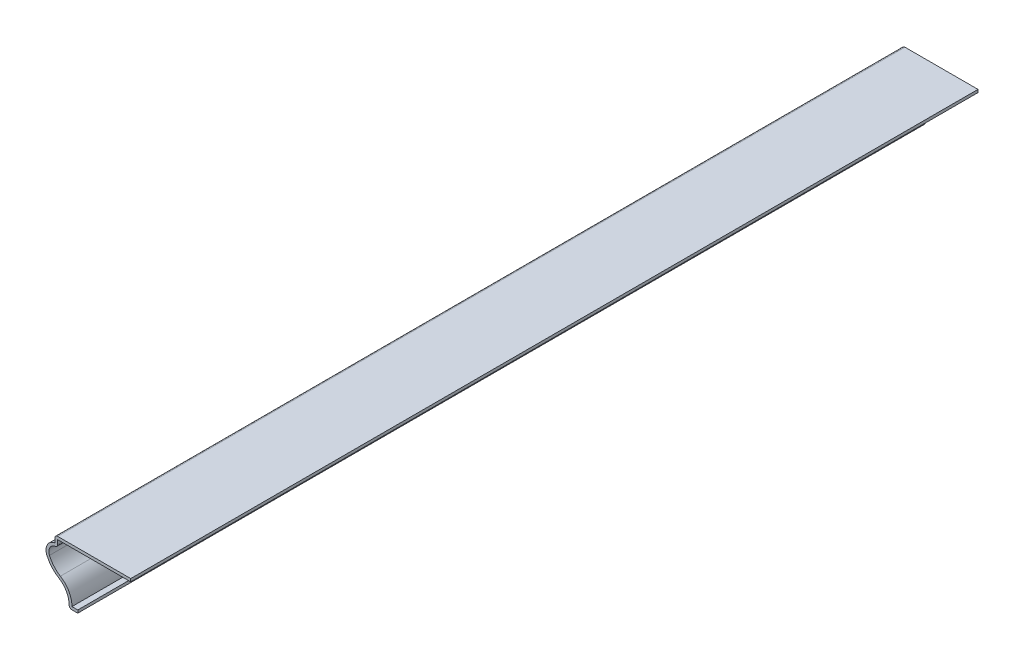
SolidWorks part; units mm, degrees
ref_plane "Front Plane" through (0, 0, 0) normal (0, 0, 1) x (1, 0, 0)
ref_plane "Top Plane" through (0, 0, 0) normal (0, 1, 0) x (1, 0, 0)
ref_plane "Right Plane" through (0, 0, 0) normal (1, 0, 0) x (0, 0, -1)
sketch "Sketch1" plane through (0, 0, 0) normal (0, 0, 1) x (1, 0, 0)
  line L0 (0, 0) -> (-3.9688, 0)
  line L1 (-10.3188, 22.225) -> (-10.3188, 25.4)
  line L2 (-10.3188, 25.4) -> (23.8125, 25.4)
  arc A0 (-3.9688, 0) -> (-8.4809, 9.4212) centre (-13.4087, 1.27) ccw
  arc A1 (-8.4809, 9.4212) -> (-13.9024, 15.6529) centre (-1.4998, 20.9688) cw
  arc A2 (-13.9024, 15.6529) -> (-10.3188, 22.225) centre (-9.525, 17.5291) cw
  point P9 (0, 0)
  point P12 (0, 0)
  point P13 (-17.4017, 11.8398)
  point P14 (-1.8113, 21.6197)
  point P15 (-13.8303, 15.4929)
  dimension "D2" = 4.7625
  dimension "D3" = 13.4937
  dimension "D4" = 9.525
  dimension "D1" = 34.1313
  dimension "D5" = 25.4
  dimension "D6" = 3.175
  dimension "D7" = 3.9688
  dimension "D8" = 38.1
  dimension "D9" = 10.3187
  dimension "D10" = 1.27
extrude "Extrude-Thin1" add sketch "Sketch1" against normal blind 381 thin
fillet "Fillet1" radius 1.27 3 edges at (-3.9688, 0, -190.5) (-9.0488, 20.989, -190.5) (-10.3188, 25.4, -190.5)
